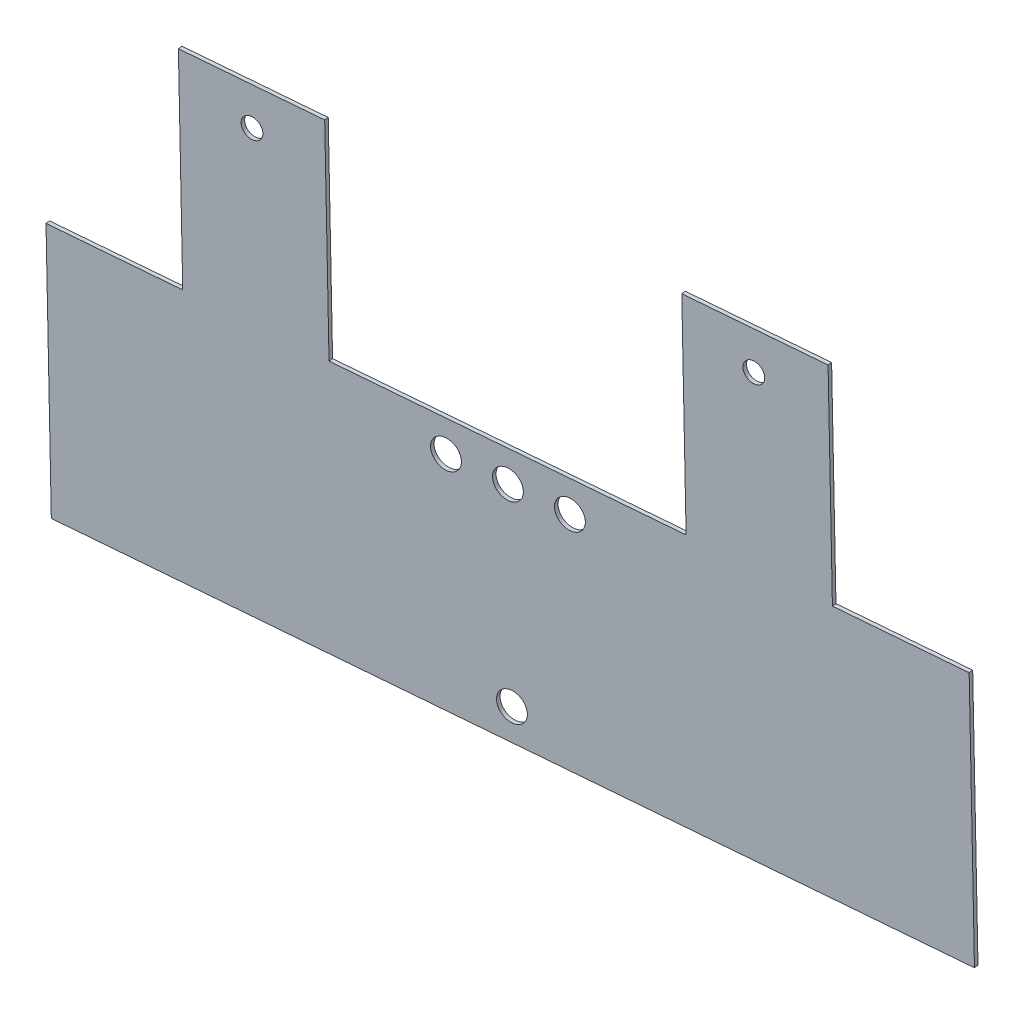
SolidWorks part; units mm, degrees
ref_plane "Front Plane" through (0, 0, 0) normal (0, 0, 1) x (1, 0, 0)
ref_plane "Top Plane" through (0, 0, 0) normal (0, 1, 0) x (1, 0, 0)
ref_plane "Right Plane" through (0, 0, 0) normal (1, 0, 0) x (0, 0, -1)
sketch "Sketch1" plane through (16.9972, -4.1499, 204.6314) normal (-0.0828, 0.0202, -0.9964) x (0.9966, 0.002, -0.0827)
  line L0 (-405.6316, 283.217) -> (-385.6926, 283.217)
  line L1 (-520.3126, 323.857) -> (-500.3736, 323.857)
  line L2 (-520.3126, 323.857) -> (-520.3126, 283.217)
  line L3 (-520.3126, 283.217) -> (-500.3736, 283.217)
  line L4 (-385.6926, 323.857) -> (-385.6926, 283.217)
  line L6 (-426.9676, 283.217) -> (-426.9676, 250.0037)
  line L7 (-426.9676, 250.0037) -> (-405.6316, 250.0037)
  line L8 (-405.6316, 283.217) -> (-405.6316, 250.0037)
  line L9 (-405.0144, 323.857) -> (-385.6926, 323.857)
  line L14 (-479.4985, 323.857) -> (-465.3599, 323.857)
  line L20 (-500.3736, 283.217) -> (-500.3736, 250.0037)
  line L21 (-500.3736, 250.0037) -> (-479.0376, 250.0037)
  line L22 (-479.0376, 283.217) -> (-479.0376, 250.0037)
  line L23 (-479.0376, 283.217) -> (-426.9676, 283.217)
  line L24 (-432.4144, 323.857) -> (-405.0144, 323.857)
  line L25 (-500.3736, 323.857) -> (-479.4985, 323.857)
  line L26 (-445.0971, 323.857) -> (-432.4144, 323.857)
  line L31 (-465.3599, 323.857) -> (-445.0971, 323.857)
  dimension "D1" = 134.62
  dimension "D2" = 40.64
  dimension "D3" = 21.336
  dimension "D4" = 52.07
  dimension "D5" = 33.2133
extrude "Boss-Extrude1" add sketch "Sketch1" along normal blind 0.6096
ref_plane "Plane1" through (-508.5923, -1, 42.2247) normal (0.9966, 0.002, -0.0827) x (-0.0828, 0.028, -0.9962)
sketch "Sketch5" plane through (16.9468, -4.1376, 204.024) normal (-0.0828, 0.0202, -0.9964) x (-0.9966, -0.0017, 0.0827)
  circle A1 centre (452.9566, -318.9845) radius 2.25
extrude "Cut-Extrude2" cut sketch "Sketch5" against normal up to surface (430.4201 mm away)
ref_plane "Plane2" through (0.0852, -303.4744, -6.1615) normal (0.0003, -0.9998, -0.0203) x (-1, -0.0003, 0)
mirror "Mirror1" about plane through (0.0852, -303.4744, -6.1615) normal (0.0003, -0.9998, -0.0203) of "Cut-Extrude2"
sketch "Sketch6" plane through (16.9468, -4.1376, 204.024) normal (-0.0828, 0.0202, -0.9964) x (-0.9966, -0.0017, 0.0827)
  circle A1 centre (416.5068, -256.1738) radius 1.5875
  dimension "D1" = 3.175
  dimension "D2" = 103.726
  dimension "D3" = 6.0353
extrude "Cut-Extrude5" cut sketch "Sketch6" against normal up to surface (0.6096 mm away) up to face at (-436.6564, -293.1953, 236.4512)
ref_plane "Plane3" through (-451.4485, -0.8877, 37.4805) normal (-0.9966, -0.002, 0.0827) x (0.0827, 0.0002, 0.9966)
sketch "Sketch7" plane through (16.9468, -4.1376, 204.024) normal (-0.0828, 0.0202, -0.9964) x (-0.9966, -0.0017, 0.0827)
  circle A0 centre (489.6815, -256.1944) radius 1.5875
  dimension "D1" = 3.175
  dimension "D2" = 10.7236
  dimension "D3" = 6.0559
extrude "Cut-Extrude6" cut sketch "Sketch7" against normal up to surface (0.6096 mm away) up to face at (-399.6628, -260.97, 234.0319)
sketch "Sketch8" plane through (16.9972, -4.1499, 204.6314) normal (0.0828, -0.0202, 0.9964) x (0.9966, 0.0017, -0.0827)
  circle A0 centre (-443.9257, -288.342) radius 2.25
  circle A1 centre (-960.2704, 120.8255) radius 2.25
  circle A2 centre (-462.0048, -288.3471) radius 2.25
extrude "Cut-Extrude7" cut sketch "Sketch8" against normal blind 2.54
